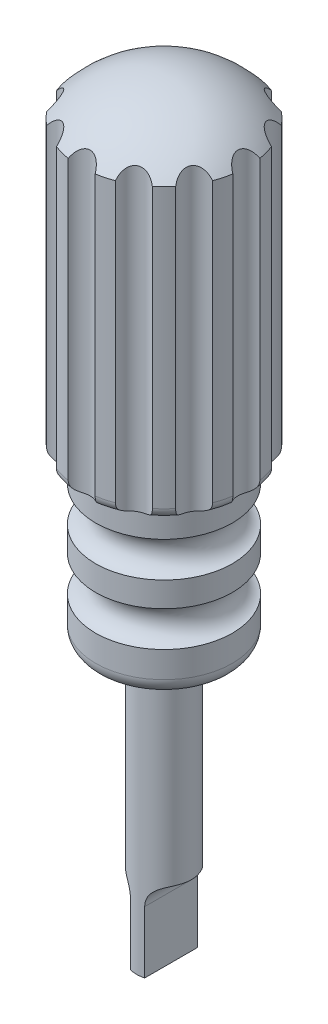
SolidWorks part; units mm, degrees
ref_plane "정면" through (0, 0, 0) normal (0, 0, 1) x (1, 0, 0)
ref_plane "윗면" through (0, 0, 0) normal (0, 1, 0) x (1, 0, 0)
ref_plane "우측면" through (0, 0, 0) normal (1, 0, 0) x (0, 0, -1)
sketch "스케치3" plane through (0, 0, 0) normal (0, 0, 1) x (1, 0, 0)
  line L0 (0, 140) -> (0, 0) construction
  line L1 (-15.25, 133) -> (-15.25, 80)
  line L2 (-15.25, 80) -> (-12.5, 80)
  line L3 (-12.5, 80) -> (-12.5, 50)
  line L4 (-12.5, 50) -> (-5, 50)
  line L5 (-5, 50) -> (-5, 0)
  line L6 (-5, 0) -> (0, 0)
  line L7 (0, 140) -> (0, 0)
  arc A0 (0, 140) -> (-15.25, 133) centre (0, 119.8884) ccw
  point P3 (0, 0)
  point P6 (-8.75, 50)
  point P12 (0, 0)
  dimension "D1" = 140
  dimension "D2" = 7
  dimension "D3" = 5
  dimension "D4" = 15.25
  dimension "D6" = 80
  dimension "D7" = 50
  dimension "D8" = 25
revolve "회전1" add sketch "스케치3" angle 360 about L0
sketch "스케치4" plane through (0, 0, 0) normal (0, 0, 1) x (1, 0, 0)
  line L0 (-12.5, 50) -> (12.5, 50) construction
  circle A0 centre (13.2, 61) radius 3.3
  circle A1 centre (13.2, 72) radius 3.3
  point P2 (0, 0)
  point P8 (28.8619, 75.6662)
  point P9 (0, 0)
  point P10 (0, 0)
  dimension "D1" = 6.6
  dimension "D6" = 6.6
  dimension "D2" = 0.7
  dimension "D3" = 11
  dimension "D4" = 0.7
  dimension "D5" = 11
ref_axis "기준축1" through (0, 80, 0) along (0, 1, 0)
revolve "컷-회전1" cut sketch "스케치4" angle 360 about axis through (0, 80, 0) along (0, 1, 0)
fillet "필렛1" radius 2 1 edges at (0, 80, 15.25)
fillet "필렛2" radius 3 1 edges at (0, 50, 12.5)
sketch "스케치6" plane through (0, 0, 0) normal (0, 1, 0) x (1, 0, 0)
  circle A0 centre (0, 16.26) radius 2.75
  point P2 (0, 0)
  point P3 (-8.7652, 23.3738)
  point P5 (0, 0)
  dimension "D1" = 5.5
  dimension "D2" = 0
  dimension "D3" = 16.26
extrude "컷-돌출2" cut sketch "스케치6" along normal through all both and the other way through all
pattern_circular "원형 패턴1" count 12 over 360 about axis through (0, 0, 0) along (0, 1, 0) of "컷-돌출2"
sketch "스케치7" plane through (0, 0, 0) normal (0, 0, 1) x (1, 0, 0)
  line L0 (1.3, 0) -> (1.3, 11.3)
  line L1 (-5, 0) -> (5, 0) construction
  line L2 (5, 0) -> (5, 50) construction
  line L3 (5, 15) -> (11.3, 15)
  line L4 (11.3, 15) -> (11.3, 0)
  line L5 (11.3, 0) -> (1.3, 0)
  line L6 (0, 0) -> (0, 21.0775) construction
  line L7 (-11.3, 0) -> (-1.3, 0)
  line L8 (-11.3, 15) -> (-11.3, 0)
  line L9 (-5, 15) -> (-11.3, 15)
  line L10 (-1.3, 0) -> (-1.3, 11.3)
  arc A0 (1.3, 11.3) -> (5, 15) centre (5, 11.3) cw
  arc A1 (-1.3, 11.3) -> (-5, 15) centre (-5, 11.3) ccw
  dimension "D2" = 3.7
  dimension "D1" = 1.3
  dimension "D3" = 15
  dimension "D4" = 10
extrude "컷-돌출3" cut sketch "스케치7" against normal through all both and the other way through all
